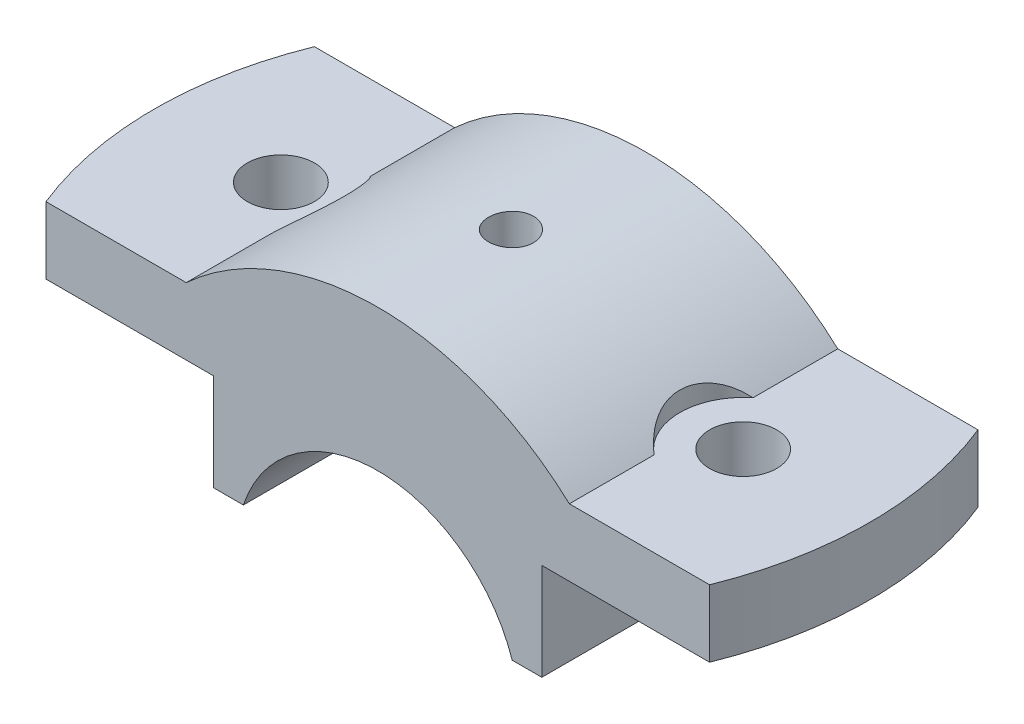
SolidWorks part; units mm, degrees
ref_plane "Front Plane" through (0, 0, 0) normal (0, 0, 1) x (1, 0, 0)
ref_plane "Top Plane" through (0, 0, 0) normal (0, 1, 0) x (1, 0, 0)
ref_plane "Right Plane" through (0, 0, 0) normal (1, 0, 0) x (0, 0, -1)
sketch "Sketch1" plane through (0, 0, 0) normal (0, 0, 1) x (1, 0, 0)
  line L0 (0, 65.7674) -> (0, -72.4218) construction
  line L1 (-90.9431, 0) -> (99.5938, 0) construction
  line L2 (-18.0278, 6) -> (-22, 6)
  line L3 (-22, 6) -> (-22, 19)
  line L4 (-22, 19) -> (-50, 19)
  line L5 (-50, 19) -> (-50, 28)
  line L6 (-50, 28) -> (-25.6905, 28)
  line L7 (0, 38) -> (0, 19)
  arc A0 (-18.0278, 6) -> (0, 19) centre (0, 0) cw
  arc A1 (-25.6905, 28) -> (0, 38) centre (0, 0) cw
  dimension "D1" = 19
  dimension "D6" = 9
  dimension "D5" = 38
  dimension "D2" = 22
  dimension "D3" = 6
  dimension "D4" = 19
  dimension "D7" = 50
extrude "Boss-Extrude1" add sketch "Sketch1" against normal mid plane 36
mirror "Mirror1" about plane through (0, 0, 0) normal (1, 0, 0) of "Boss-Extrude1"
hole_wizard "Ø6.0mm Dowel Hole2" positions "Sketch22" profile "Sketch23" hole size "Ø6.0" standard "ANSI Metric" end condition through all
sketch "Sketch22" plane through (0, 28, 0) normal (0, 1, 0) x (1, 0, 0)
  point P0 (-31, 0)
  dimension "D1" = 31
sketch "Sketch23" plane through (-31, 28, 0) normal (1, 0, 0) x (0, 0, 1)
  line L0 (0, 0) -> (0, 22)
  line L1 (0, 22) -> (4.5, 22)
  line L2 (4.5, 22) -> (4.5, 0)
  line L5 (4.5, 0) -> (0, 0)
  line L11 (0, -6.35) -> (0, 107.95) construction
  dimension "Thru Hole Dia." = 9
  dimension "Thru Hole Depth" = 22
sketch "Sketch24" plane through (0, 28, 0) normal (0, 1, 0) x (1, 0, 0)
  circle A0 centre (-31, 0) radius 8.5
extrude "Cut-Extrude7" cut sketch "Sketch24" along normal blind 19
mirror "Mirror5" about plane through (0, 0, 0) normal (1, 0, 0) of "Cut-Extrude7"
sketch "Sketch25" plane through (0, 28, 0) normal (0, 1, 0) x (1, 0, 0)
  line L0 (-25.6905, -18) -> (-50, -18) construction
  line L1 (-25.6905, 18) -> (-50, 18) construction
  line L2 (-44.4972, 18) -> (-50, 18)
  line L3 (-50, 18) -> (-50, -18)
  line L4 (-50, -18) -> (-44.4972, -18)
  arc A0 (-44.4972, -18) -> (-44.4972, 18) centre (0, 0) cw
  dimension "D1" = 48
extrude "Cut-Extrude8" cut sketch "Sketch25" against normal through all
mirror "Mirror7" about plane through (0, 0, 0) normal (1, 0, 0) of "Cut-Extrude8"
hole_wizard "CBORE for M6 Hex Head Machine Screw1" positions "3DSketch5" profile "Sketch28" counterbore size "M6" standard "ANSI Metric" end condition through all
sketch3d "3DSketch5"
  point P0 (-0.1464, 37.9997, 0)
  dimension "D1" = 0
sketch "Sketch28" plane through (-0.1464, 37.9997, 0) normal (0, 0, 1) x (-1, -0.0039, 0)
  line L0 (0, 0) -> (0, 32.1849)
  line L1 (0, 32.1849) -> (2.5, 32.1849)
  line L2 (2.5, 13.825) -> (2.5, 32.1849)
  line L3 (2.5, 13.825) -> (3.325, 13)
  line L4 (3.325, 13) -> (3, 13)
  line L5 (3, 13) -> (3, 0)
  line L7 (0, 0) -> (3, 0)
  line L9 (-2.5, 13.825) -> (-3.325, 13) construction
  line L11 (0, -6.35) -> (0, 107.95) construction
  dimension "Thru Hole Dia." = 5
  dimension "Thru Hole Depth" = 32.1849
  dimension "C'Bore Dia." = 6
  dimension "C'Bore Depth" = 13
  dimension "Mid C'Sink Dia." = 6.65
  dimension "Mid C'Sink Angle" = 90
hole_wizard "Ø6.0mm Dowel Hole3" positions "Sketch30" profile "Sketch31" hole size "Ø6.0" standard "ANSI Metric" end condition through all
sketch "Sketch30" plane through (0, 28, 0) normal (0, 1, 0) x (1, 0, 0)
  point P0 (31, 0)
  dimension "D1" = 31
sketch "Sketch31" plane through (31, 28, 0) normal (1, 0, 0) x (0, 0, 1)
  line L0 (0, 0) -> (0, 22)
  line L1 (0, 22) -> (4.5, 22)
  line L2 (4.5, 22) -> (4.5, 0)
  line L5 (4.5, 0) -> (0, 0)
  line L11 (0, -6.35) -> (0, 107.95) construction
  dimension "Thru Hole Dia." = 9
  dimension "Thru Hole Depth" = 22
